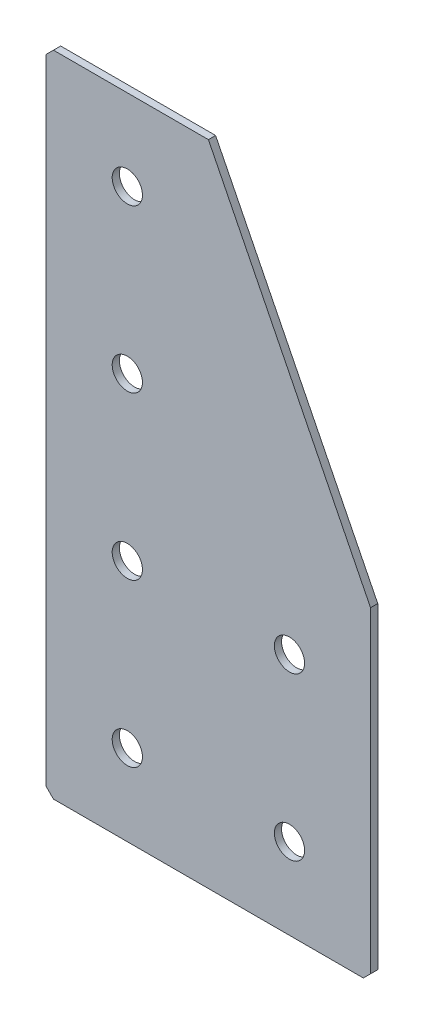
SolidWorks part; units mm, degrees
material "Простая углеродистая сталь"
ref_plane "Спереди(Плоскость XY)" through (0, 0, 0) normal (0, 0, 1) x (1, 0, 0)
ref_plane "Сверху(Плоскость XZ)" through (0, 0, 0) normal (0, 1, 0) x (1, 0, 0)
ref_plane "Справа(Плоскость ZY)" through (0, 0, 0) normal (1, 0, 0) x (0, 0, -1)
sketch "Эскиз1" plane through (0, 0, 0) normal (0, 0, -1) x (1, 0, 0)
  line L0 (0, 0) -> (0, 180)
  line L1 (0, 180) -> (90, 180)
  line L2 (90, 180) -> (90, 90)
  line L3 (90, 90) -> (45, 90) construction
  line L4 (45, 90) -> (45, 0) construction
  line L5 (45, 0) -> (0, 0)
  line L6 (90, 90) -> (45, 0)
  dimension "D1" = 180
  dimension "D2" = 90
  dimension "D3" = 45
  dimension "D4" = 45
extrude "Бобышка-Вытянуть1" add sketch "Эскиз1" along normal blind 2
hole_wizard "Отверстие с зазором M81" positions "Эскиз2" profile "Эскиз3" hole size "M8" standard "DIN" end condition up to next
sketch "Эскиз2" plane through (0, 0, -2) normal (0, 0, -1) x (1, 0, 0)
  line L0 (22.5, 0) -> (22.5, 180) construction
  line L1 (0, 0) -> (45, 0) construction
  line L2 (90, 180) -> (0, 180) construction
  point P0 (22.5, 157.5)
  point P2 (22.5, 112.5)
  point P4 (22.5, 67.5)
  point P6 (22.5, 22.5)
  point P27 (67.5, 157.5)
  point P29 (67.5, 112.5)
  dimension "D1" = 45
  dimension "D2" = 45
  dimension "D3" = 45
  dimension "D4" = 22.5
  dimension "D5" = 45
sketch "Эскиз3" plane through (22.5, -157.5, -2) normal (1, 0, 0) x (0, 1, 0)
  line L0 (0, 0) -> (0, 2)
  line L1 (0, 2) -> (4.2, 2)
  line L2 (4.2, 2) -> (4.2, 0)
  line L5 (4.2, 0) -> (0, 0)
  line L11 (0, -6.35) -> (0, 107.95) construction
  dimension "Диаметр сквозного отверстия" = 8.4
  dimension "Глубина сквозного отверстия" = 2
chamfer "Фаска1" distance 2 angle 45 3 edges at (0, 0, -1) (90, -180, -1) (0, -180, -1)
